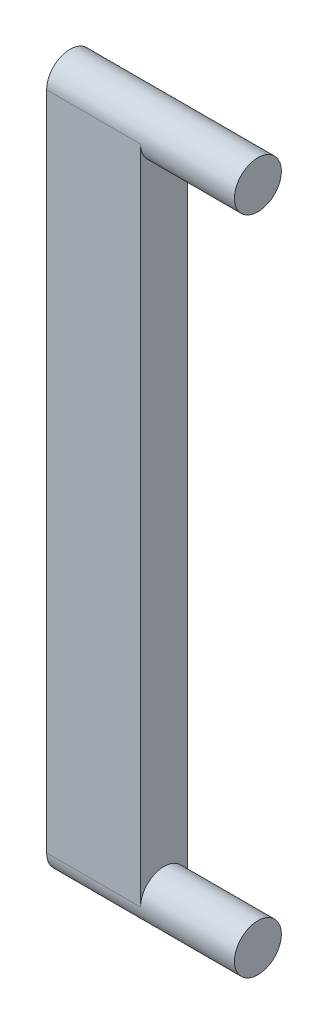
SolidWorks part; units mm, degrees
ref_plane "Plan de face" through (0, 0, 0) normal (0, 0, 1) x (1, 0, 0)
ref_plane "Plan de dessus" through (0, 0, 0) normal (0, 1, 0) x (1, 0, 0)
ref_plane "Plan de droite" through (0, 0, 0) normal (1, 0, 0) x (0, 0, -1)
sketch "Esquisse1" plane through (0, 0, 0) normal (1, 0, 0) x (0, 0, -1)
  circle A0 centre (0, 0) radius 2.5
  dimension "D1" = 5
extrude "Boss.-Extru.1" add sketch "Esquisse1" against normal blind 10
sketch "Esquisse2" plane through (-10, 0, 0) normal (-1, 0, 0) x (0, 0, 1)
  line L0 (-2.5, 0) -> (-2.5, -70.37)
  line L2 (2.5, -70.37) -> (2.5, 0)
  arc A0 (2.5, 0) -> (-2.5, 0) centre (0, 0) ccw
  circle A1 centre (0, 0) radius 2.5 construction
  arc A2 (-2.5, -70.37) -> (2.5, -70.37) centre (0, -70.37) ccw
  dimension "D1" = 70.37
extrude "Boss.-Extru.2" add sketch "Esquisse2" along normal blind 10
sketch "Esquisse4" plane through (-10, 0, 0) normal (1, 0, 0) x (0, 0, -1)
  circle A0 centre (0, -70.37) radius 2.5
  dimension "D1" = 5
extrude "Boss.-Extru.4" add sketch "Esquisse4" along normal blind 10
